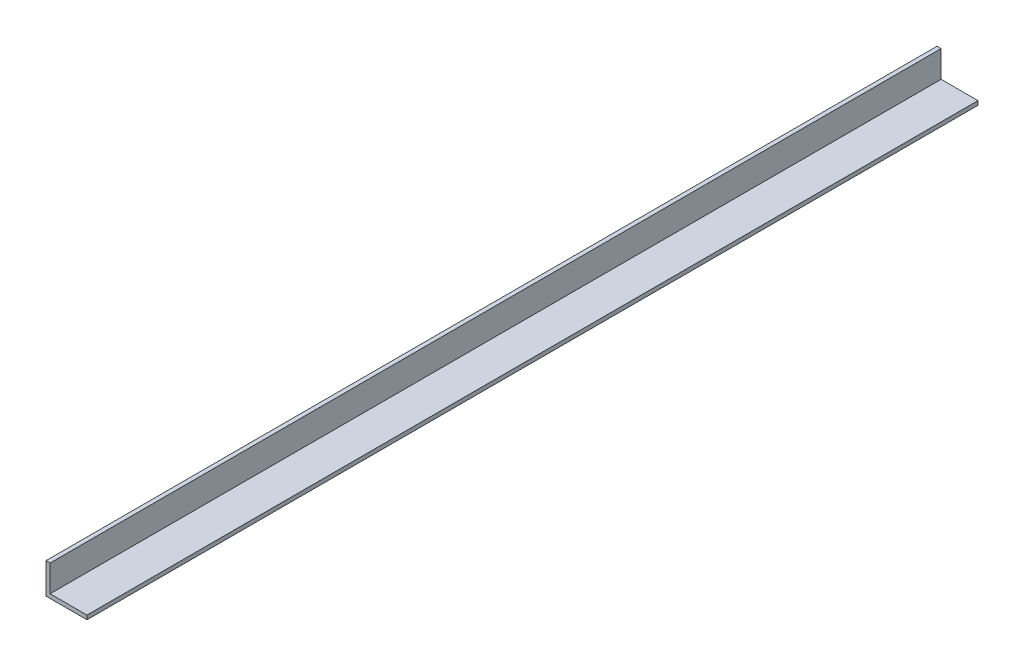
SolidWorks part; units mm, degrees
ref_plane "前视基准面" through (0, 0, 0) normal (0, 0, 1) x (1, 0, 0)
ref_plane "上视基准面" through (0, 0, 0) normal (0, 1, 0) x (1, 0, 0)
ref_plane "右视基准面" through (0, 0, 0) normal (1, 0, 0) x (0, 0, -1)
sketch "草图1" plane through (0, 0, 0) normal (0, 0, 1) x (1, 0, 0)
  line L0 (0, 15) -> (0, 0)
  line L1 (0, 0) -> (20, 0)
  line L2 (20, 0) -> (20, 2)
  line L3 (20, 2) -> (2, 2)
  line L4 (2, 2) -> (2, 15)
  line L5 (0, 15) -> (2, 15)
  dimension "D1" = 2
  dimension "D2" = 2
  dimension "D3" = 15
  dimension "D4" = 20
extrude "凸台-拉伸1" add sketch "草图1" along normal mid plane 435
